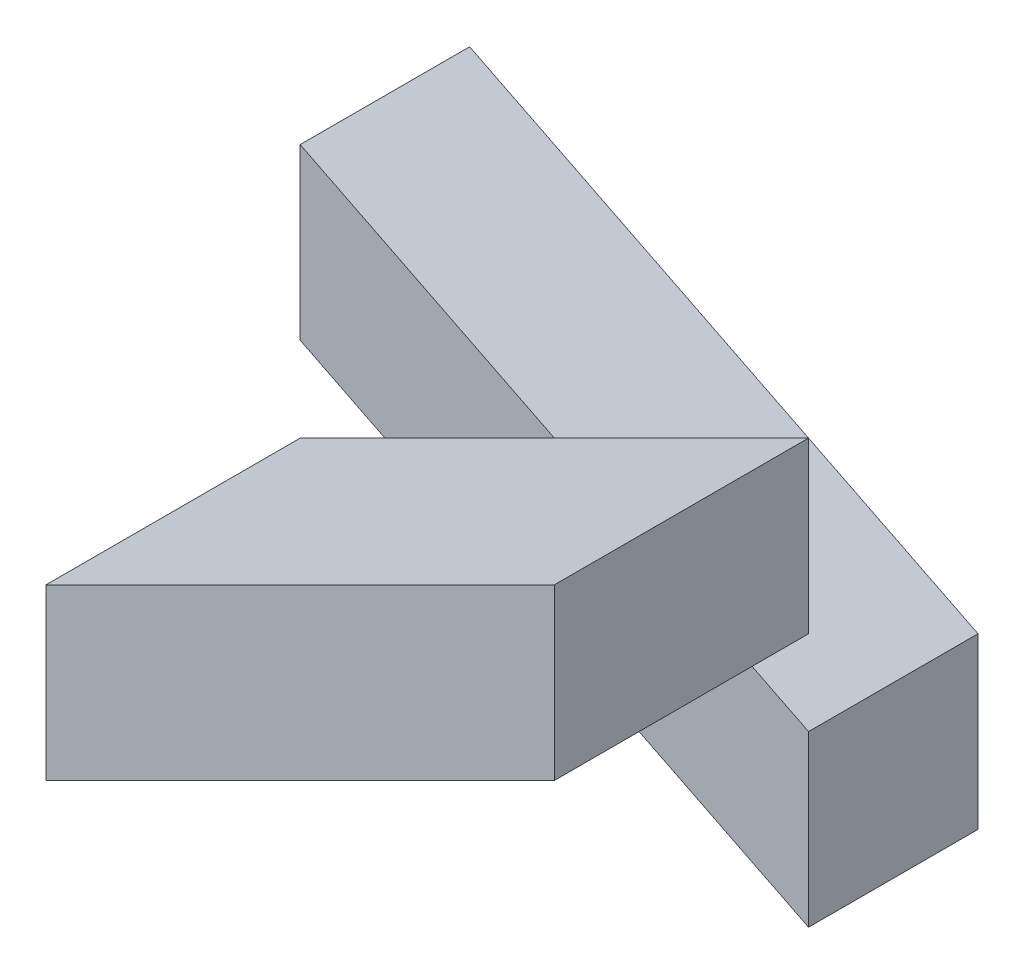
SolidWorks part; units mm, degrees
ref_plane "Front Plane" through (0, 0, 0) normal (0, 0, 1) x (1, 0, 0)
ref_plane "Top Plane" through (0, 0, 0) normal (0, 1, 0) x (1, 0, 0)
ref_plane "Right Plane" through (0, 0, 0) normal (1, 0, 0) x (0, 0, -1)
sketch "Sketch1" plane through (0, 0, 0) normal (0, 0, 1) x (1, 0, 0)
  line L0 (-39.9083, 15.0917) -> (-39.9083, 5.0917)
  line L1 (-39.9083, 5.0917) -> (-9.9083, -9.9083)
  line L2 (-9.9083, -9.9083) -> (-9.9083, 0.0917)
  line L3 (-9.9083, 0.0917) -> (-39.9083, 15.0917)
  dimension "D1" = 10
  dimension "D2" = 10
  dimension "D3" = 30
  dimension "D4" = 15
extrude "Boss-Extrude1" add sketch "Sketch1" along normal blind 10
sketch "Sketch2" plane through (0, 0, 10) normal (0, 0, 1) x (1, 0, 0)
  line L0 (-9.9083, 15.0917) -> (-9.9083, 5.0917)
  line L1 (-9.9083, 5.0917) -> (-39.9083, -9.9083)
  line L2 (-39.9083, -9.9083) -> (-39.9083, 0.0917)
  line L3 (-39.9083, 0.0917) -> (-9.9083, 15.0917)
  dimension "D1" = 10
  dimension "D2" = 15
extrude "Boss-Extrude3" add sketch "Sketch2" along normal blind 15
